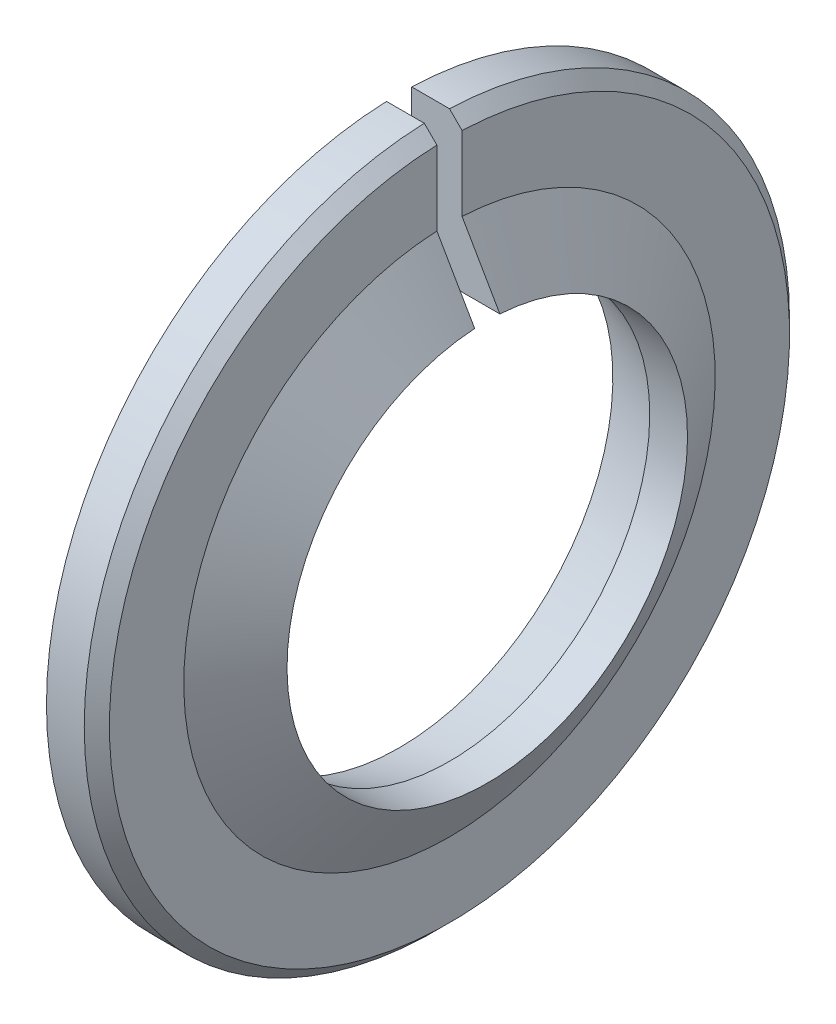
SolidWorks part; units mm, degrees
material "Сплав 3М ОСТ 1.92077-91"
ref_plane "Plane1" through (0, 0, 0) normal (0, 0, 1) x (1, 0, 0)
ref_plane "Plane2" through (0, 0, 0) normal (0, 1, 0) x (1, 0, 0)
ref_plane "Plane3" through (0, 0, 0) normal (1, 0, 0) x (0, 0, -1)
sketch "Эскиз1" plane through (0, 0, 0) normal (0, 0, 1) x (1, 0, 0)
  line L0 (-6.1768, 0) -> (6.1768, 0) construction
  line L1 (0, 7.95) -> (1.5, 7.95)
  line L2 (0, 7.95) -> (-2, 8.4859)
  line L3 (0, 14) -> (0, 10.5481)
  line L4 (1.5, 7.95) -> (0, 10.5481)
  line L5 (-2, 14) -> (0, 14)
  line L6 (-2, 14) -> (-2, 8.4859)
  dimension "D1" = 15.9
  dimension "D2" = 28
  dimension "D3" = 2
  dimension "D4" = 60
  dimension "D5" = 15
  dimension "D6" = 1.5
  dimension "D7" = 3.5
revolve "Повернуть1" add sketch "Эскиз1" angle 360 about L0
chamfer "Фаска1" distance 0.5 angle 45 1 edges at (0, 0, 14)
sketch "Эскиз2" plane through (-2, 0, 0) normal (-1, 0, 0) x (0, 0, 1)
  line L0 (0.5, 0) -> (-0.5, 0)
  line L1 (-0.5, 0) -> (-0.5, 14.5)
  line L2 (0, 0) -> (0, 5.424) construction
  line L3 (0.5, 0) -> (0.5, 14.5)
  line L4 (-0.5, 14.5) -> (0.5, 14.5)
  circle A1 centre (0, 0) radius 14 construction
  point P9 (0, 14)
  dimension "D1" = 0.5
  dimension "D2" = 14
extrude "Вырез-Вытянуть2" cut sketch "Эскиз2" against normal through all contours L1 L4 L3 L0
